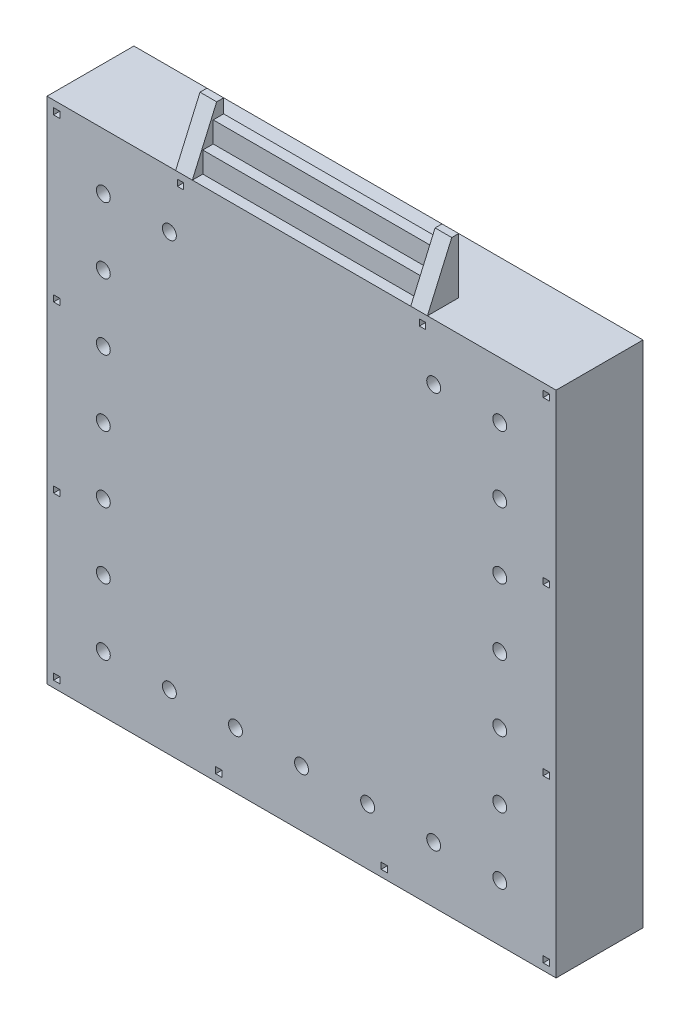
SolidWorks part; units mm, degrees
ref_plane "前视基准面" through (0, 0, 0) normal (0, 0, 1) x (1, 0, 0)
ref_plane "上视基准面" through (0, 0, 0) normal (0, 1, 0) x (1, 0, 0)
ref_plane "右视基准面" through (0, 0, 0) normal (1, 0, 0) x (0, 0, -1)
sketch "草图1" plane through (0, 0, 0) normal (0, 0, 1) x (1, 0, 0)
  line L1 (-2345.2315, 6358.0459) -> (4974.7685, 6358.0459)
  line L2 (-2345.2315, 6358.0459) -> (-2345.2315, -961.9541)
  line L3 (-2345.2315, -961.9541) -> (4974.7685, -961.9541)
  line L4 (4974.7685, 6358.0459) -> (4974.7685, -961.9541)
  dimension "D1" = 7320
  dimension "D2" = 7320
extrude "凸台-拉伸1" add sketch "草图1" against normal blind 1250
sketch "草图2" plane through (0, 0, 0) normal (0, 0, 1) x (1, 0, 0)
  line L0 (-2345.2315, 6358.0459) -> (-2345.2315, -961.9541) construction
  line L2 (4974.7685, 6358.0459) -> (-2345.2315, 6358.0459) construction
  line L3 (-2345.2315, -961.9541) -> (4974.7685, -961.9541) construction
  line L4 (4974.7685, -961.9541) -> (4974.7685, 6358.0459) construction
  circle A0 centre (-1535.2315, 5548.0459) radius 100
  circle A1 centre (4164.7685, 5548.0459) radius 100
  circle A2 centre (-1535.2315, -151.9541) radius 100
  circle A3 centre (4164.7685, -151.9541) radius 100
  dimension "D9" = 200
  dimension "D10" = 200
  dimension "D11" = 200
  dimension "D12" = 200
  dimension "D1" = 810
  dimension "D2" = 810
  dimension "D3" = 810
  dimension "D4" = 810
  dimension "D5" = 810
  dimension "D6" = 810
  dimension "D7" = 810
  dimension "D8" = 810
extrude "切除-拉伸2" cut sketch "草图2" against normal blind 150
sketch "草图4" plane through (0, 6358.0459, 0) normal (0, 1, 0) x (1, 0, 0)
  line L0 (2884.7685, 1250) -> (2884.7685, 0)
  line L1 (4974.7685, 0) -> (-2345.2315, 0) construction
  line L2 (4974.7685, 1250) -> (-2345.2315, 1250) construction
  line L3 (1314.7685, 0) -> (3124.7685, 0)
  line L4 (3124.7685, 0) -> (3124.7685, 1250)
  line L5 (3124.7685, 1250) -> (-495.2315, 1250)
  line L6 (-495.2315, 1250) -> (-495.2315, 0)
  line L7 (-495.2315, 0) -> (1314.7685, 0)
  dimension "D1" = 1810
  dimension "D2" = 1810
  dimension "D3" = 240
sketch "草图9" plane through (0, 0, 0) normal (0, 0, 1) x (1, 0, 0)
  line L0 (4974.7685, -961.9541) -> (4974.7685, 6358.0459) construction
  line L1 (-2160.2315, 6173.0459) -> (-2250.2315, 6173.0459)
  line L2 (-2160.2315, 6173.0459) -> (-2160.2315, 6263.0459)
  line L3 (-2160.2315, 6263.0459) -> (-2250.2315, 6263.0459)
  line L4 (-2250.2315, 6173.0459) -> (-2250.2315, 6263.0459)
  line L5 (-2160.2315, 3843.0459) -> (-2250.2315, 3843.0459)
  line L6 (-2160.2315, 3843.0459) -> (-2160.2315, 3933.0459)
  line L7 (-2160.2315, 3933.0459) -> (-2250.2315, 3933.0459)
  line L8 (-2250.2315, 3843.0459) -> (-2250.2315, 3933.0459)
  line L9 (-2160.2315, 1463.0459) -> (-2250.2315, 1463.0459)
  line L10 (-2160.2315, 1463.0459) -> (-2160.2315, 1553.0459)
  line L11 (-2160.2315, 1553.0459) -> (-2250.2315, 1553.0459)
  line L12 (-2250.2315, 1463.0459) -> (-2250.2315, 1553.0459)
  line L13 (-2160.2315, -866.9541) -> (-2250.2315, -866.9541)
  line L14 (-2160.2315, -866.9541) -> (-2160.2315, -776.9541)
  line L15 (-2160.2315, -776.9541) -> (-2250.2315, -776.9541)
  line L16 (-2250.2315, -866.9541) -> (-2250.2315, -776.9541)
  line L17 (169.7685, -866.9541) -> (79.7685, -866.9541)
  line L18 (169.7685, -866.9541) -> (169.7685, -776.9541)
  line L19 (169.7685, -776.9541) -> (79.7685, -776.9541)
  line L20 (79.7685, -866.9541) -> (79.7685, -776.9541)
  line L21 (2549.7685, -866.9541) -> (2459.7685, -866.9541)
  line L22 (2549.7685, -866.9541) -> (2549.7685, -776.9541)
  line L23 (2549.7685, -776.9541) -> (2459.7685, -776.9541)
  line L24 (2459.7685, -866.9541) -> (2459.7685, -776.9541)
  line L25 (4879.7685, -866.9541) -> (4789.7685, -866.9541)
  line L26 (4879.7685, -866.9541) -> (4879.7685, -776.9541)
  line L27 (4879.7685, -776.9541) -> (4789.7685, -776.9541)
  line L28 (4789.7685, -866.9541) -> (4789.7685, -776.9541)
  line L29 (4879.7685, 1463.0459) -> (4789.7685, 1463.0459)
  line L30 (4879.7685, 1463.0459) -> (4879.7685, 1553.0459)
  line L31 (4879.7685, 1553.0459) -> (4789.7685, 1553.0459)
  line L32 (4789.7685, 1463.0459) -> (4789.7685, 1553.0459)
  line L33 (4879.7685, 3843.0459) -> (4789.7685, 3843.0459)
  line L34 (4879.7685, 3843.0459) -> (4879.7685, 3933.0459)
  line L35 (4879.7685, 3933.0459) -> (4789.7685, 3933.0459)
  line L36 (4789.7685, 3843.0459) -> (4789.7685, 3933.0459)
  line L37 (4879.7685, 6173.0459) -> (4789.7685, 6173.0459)
  line L38 (4879.7685, 6173.0459) -> (4879.7685, 6263.0459)
  line L39 (4879.7685, 6263.0459) -> (4789.7685, 6263.0459)
  line L40 (4789.7685, 6173.0459) -> (4789.7685, 6263.0459)
  line L41 (3099.7685, 6173.0459) -> (3009.7685, 6173.0459)
  line L42 (3099.7685, 6173.0459) -> (3099.7685, 6263.0459)
  line L43 (3099.7685, 6263.0459) -> (3009.7685, 6263.0459)
  line L44 (3009.7685, 6173.0459) -> (3009.7685, 6263.0459)
  line L45 (-380.2315, 6173.0459) -> (-470.2315, 6173.0459)
  line L46 (-380.2315, 6173.0459) -> (-380.2315, 6263.0459)
  line L47 (-380.2315, 6263.0459) -> (-470.2315, 6263.0459)
  line L48 (-470.2315, 6173.0459) -> (-470.2315, 6263.0459)
  line L49 (4974.7685, 6358.0459) -> (-2345.2315, 6358.0459) construction
  line L50 (-2345.2315, 6358.0459) -> (-2345.2315, -961.9541) construction
  line L51 (-2345.2315, -961.9541) -> (4974.7685, -961.9541) construction
  point P54 (3054.7685, 6263.0459)
  point P57 (-2205.2315, 3933.0459)
  dimension "D1" = 95
  dimension "D2" = 95
  dimension "D3" = 95
  dimension "D4" = 95
  dimension "D5" = 90
  dimension "D6" = 90
  dimension "D7" = 90
  dimension "D8" = 90
  dimension "D9" = 90
  dimension "D10" = 90
  dimension "D11" = 90
  dimension "D12" = 90
  dimension "D13" = 90
  dimension "D14" = 90
  dimension "D15" = 90
  dimension "D16" = 90
  dimension "D17" = 90
  dimension "D18" = 90
  dimension "D19" = 90
  dimension "D20" = 90
  dimension "D21" = 90
  dimension "D22" = 90
  dimension "D23" = 90
  dimension "D24" = 90
  dimension "D25" = 90
  dimension "D26" = 90
  dimension "D27" = 90
  dimension "D28" = 90
  dimension "D29" = 95
  dimension "D30" = 95
  dimension "D31" = 2240
  dimension "D32" = 95
  dimension "D33" = 95
  dimension "D34" = 95
  dimension "D35" = 95
  dimension "D36" = 2240
  dimension "D37" = 95
  dimension "D38" = 95
  dimension "D39" = 95
  dimension "D40" = 95
  dimension "D41" = 95
  dimension "D42" = 95
  dimension "D43" = 2240
  dimension "D44" = 2290
  dimension "D45" = 2240
  dimension "D46" = 2240
  dimension "D47" = 1690
  dimension "D48" = 1690
extrude "切除-拉伸3" cut sketch "草图9" against normal blind 150
sketch "草图10" plane through (0, 0, 0) normal (0, 0, 1) x (1, 0, 0)
  line L0 (-1535.2315, 5548.0459) -> (4164.7685, 5548.0459) construction
  line L1 (4164.7685, 5548.0459) -> (4164.7685, -151.9541) construction
  line L2 (4164.7685, -151.9541) -> (-1535.2315, -151.9541) construction
  line L3 (-1535.2315, -151.9541) -> (-1535.2315, 5548.0459) construction
  circle A1 centre (-585.2315, 5548.0459) radius 100
  circle A3 centre (-1535.2315, 3648.0459) radius 100
  circle A4 centre (-1535.2315, 1748.0459) radius 100
  circle A5 centre (4164.7685, 3648.0459) radius 100
  circle A6 centre (4164.7685, 1748.0459) radius 100
  circle A8 centre (3214.7685, 5548.0459) radius 100
  circle A10 centre (-1535.2315, 4598.0459) radius 100
  circle A11 centre (-1535.2315, 2698.0459) radius 100
  circle A12 centre (-1535.2315, 798.0459) radius 100
  circle A13 centre (4164.7685, 4598.0459) radius 100
  circle A14 centre (4164.7685, 2698.0459) radius 100
  circle A15 centre (4164.7685, 798.0459) radius 100
  circle A16 centre (-585.2315, -151.9541) radius 100
  circle A17 centre (364.7685, -151.9541) radius 100
  circle A18 centre (1314.7685, -151.9541) radius 100
  circle A19 centre (2264.7685, -151.9541) radius 100
  circle A20 centre (3214.7685, -151.9541) radius 100
  point P40 (-1535.2315, 5548.0459)
  point P41 (-1535.2315, -151.9541)
  point P43 (4164.7685, -151.9541)
  point P45 (4164.7685, 5548.0459)
  dimension "D1" = 200
  dimension "D2" = 200
  dimension "D3" = 200
  dimension "D4" = 200
  dimension "D5" = 200
  dimension "D6" = 200
  dimension "D7" = 200
  dimension "D8" = 200
  dimension "D9" = 200
  dimension "D10" = 200
  dimension "D11" = 200
  dimension "D12" = 200
  dimension "D13" = 200
  dimension "D14" = 200
  dimension "D15" = 200
  dimension "D16" = 200
  dimension "D20" = 200
  dimension "D21" = 950
  dimension "D22" = 950
  dimension "D23" = 950
  dimension "D24" = 950
  dimension "D25" = 950
  dimension "D26" = 950
  dimension "D27" = 950
  dimension "D28" = 950
  dimension "D29" = 950
  dimension "D30" = 950
  dimension "D31" = 950
  dimension "D32" = 950
  dimension "D33" = 950
  dimension "D34" = 950
  dimension "D35" = 950
  dimension "D36" = 950
extrude "切除-拉伸4" cut sketch "草图10" against normal blind 150
ref_plane "基准面15" through (3124.7685, 0, 0) normal (1, 0, 0) x (0, 0, -1)
sketch "草图11" plane through (3124.7685, 0, 0) normal (1, 0, 0) x (0, 0, -1)
  line L2 (450, 7158.0459) -> (450, 6358.0459)
  line L3 (450, 6358.0459) -> (0, 6358.0459)
  line L4 (0, 6358.0459) -> (350, 7158.0459)
  line L5 (350, 7158.0459) -> (450, 7158.0459)
  dimension "D1" = 100
  dimension "D2" = 800
  dimension "D3" = 450
ref_plane "基准面16" through (-495.2315, 0, 0) normal (-1, 0, 0) x (0, 0, 1)
ref_plane "基准面19" through (2884.7685, 0, 0) normal (-1, 0, 0) x (0, 0, 1)
extrude "凸台-拉伸2" add sketch "草图11" against normal blind 3620
sketch "草图14" plane through (2884.7685, 0, 0) normal (-1, 0, 0) x (0, 0, 1)
  line L0 (0, 6358.0459) -> (-1250, 6358.0459) construction
  line L1 (-150, 6358.0459) -> (-150, 6658.0459)
  line L2 (-150, 6658.0459) -> (-300, 6658.0459)
  line L3 (-300, 6658.0459) -> (-300, 6958.0459)
  line L4 (-300, 6958.0459) -> (-450, 6958.0459)
  line L5 (-450, 6358.0459) -> (-450, 7158.0459) construction
  line L6 (-450, 6958.0459) -> (-450, 7158.0459)
  line L7 (-450, 7158.0459) -> (-350, 7158.0459)
  line L8 (-350, 7158.0459) -> (0, 6358.0459)
  line L9 (0, 6358.0459) -> (-150, 6358.0459)
  dimension "D1" = 150
  dimension "D2" = 150
  dimension "D3" = 200
  dimension "D4" = 300
extrude "切除-拉伸5" cut sketch "草图14" along normal blind 3140
